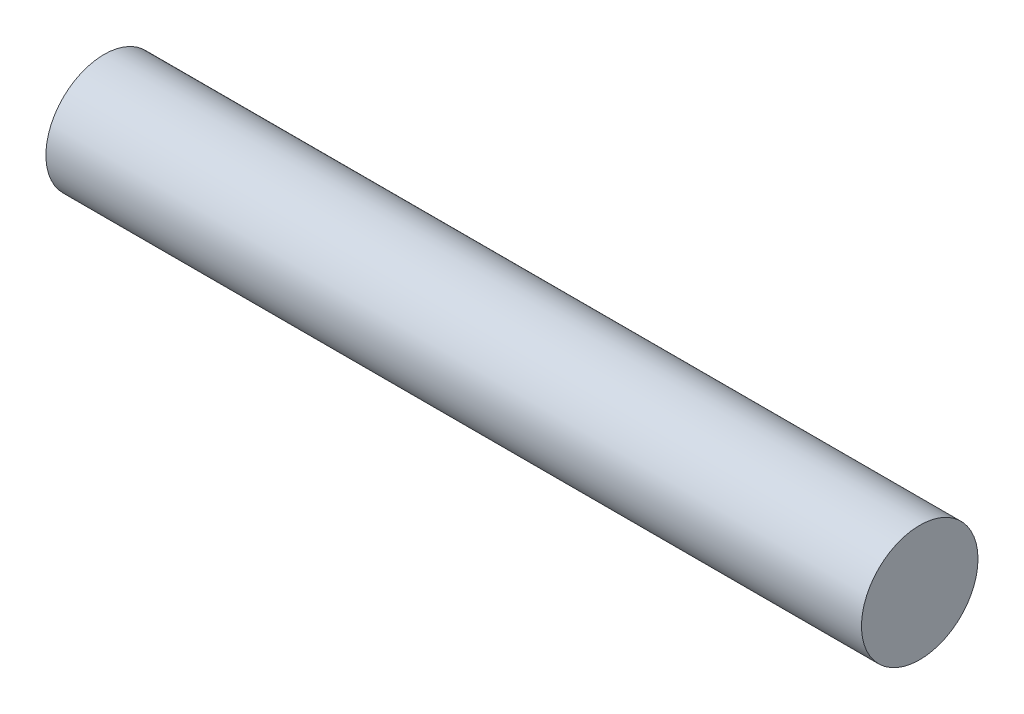
SolidWorks part; units mm, degrees
ref_plane "前视基准面" through (0, 0, 0) normal (0, 0, 1) x (1, 0, 0)
ref_plane "上视基准面" through (0, 0, 0) normal (0, 1, 0) x (1, 0, 0)
ref_plane "右视基准面" through (0, 0, 0) normal (1, 0, 0) x (0, 0, -1)
sketch "草图1" plane through (0, 0, 0) normal (1, 0, 0) x (0, 0, -1)
  circle A0 centre (0, 0) radius 2.5
  dimension "D1" = 5
extrude "凸台-拉伸1" add sketch "草图1" along normal blind 35
